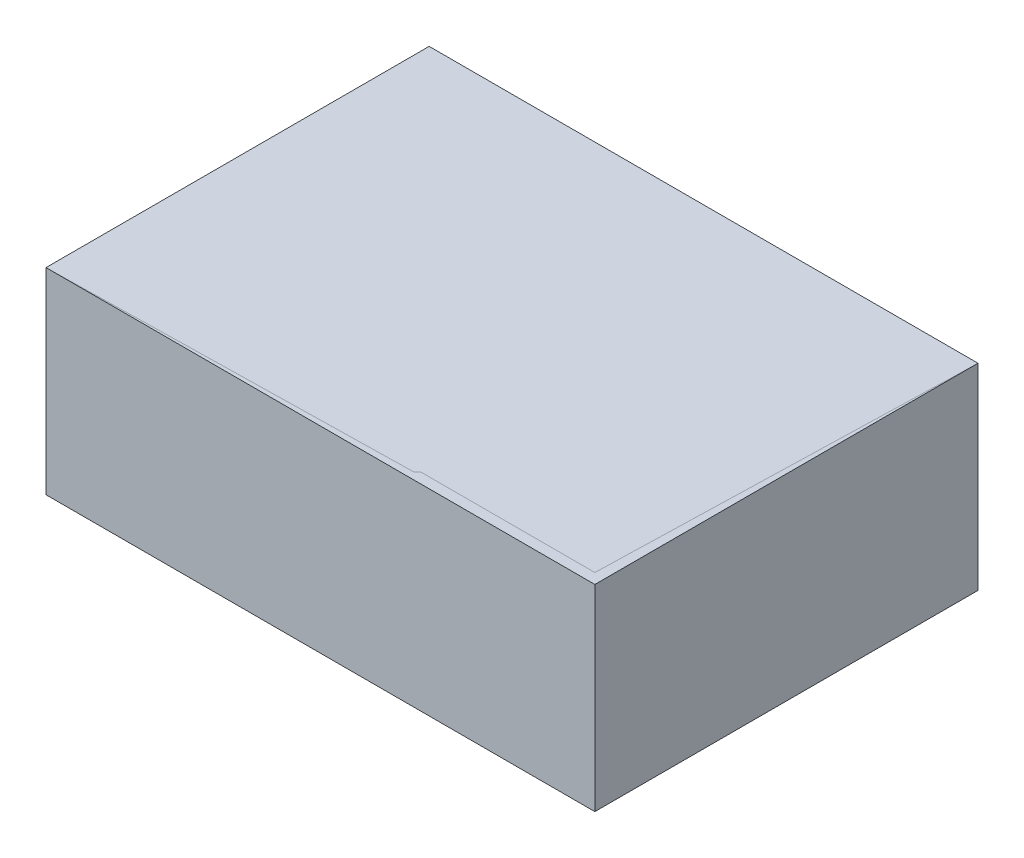
SolidWorks part; units mm, degrees
ref_plane "Front Plane" through (0, 0, 0) normal (0, 0, 1) x (1, 0, 0)
ref_plane "Top Plane" through (0, 0, 0) normal (0, 1, 0) x (1, 0, 0)
ref_plane "Right Plane" through (0, 0, 0) normal (1, 0, 0) x (0, 0, -1)
sketch "Sketch1" plane through (0, 0, 0) normal (0, 1, 0) x (1, 0, 0)
  line L1 (-132.5, -92.5) -> (132.5, -92.5)
  line L2 (-132.5, -92.5) -> (-132.5, 92.5)
  line L3 (-132.5, 92.5) -> (132.5, 92.5)
  line L4 (132.5, -92.5) -> (132.5, 92.5)
  line L5 (-132.5, -92.5) -> (132.5, 92.5) construction
  line L6 (-132.5, 92.5) -> (132.5, -92.5) construction
  point P0 (0, 0)
  dimension "D1" = 265
  dimension "D2" = 185
extrude "Boss-Extrude1" add sketch "Sketch1" along normal blind 95
sketch "Sketch2" plane through (0, 95, 0) normal (0, 1, 0) x (1, 0, 0)
  line L1 (-127.5, -87.5) -> (127.5, -87.5)
  line L2 (-127.5, -87.5) -> (-127.5, 87.5)
  line L3 (-127.5, 87.5) -> (127.5, 87.5)
  line L4 (127.5, -87.5) -> (127.5, 87.5)
  line L5 (-127.5, -87.5) -> (127.5, 87.5) construction
  line L6 (-127.5, 87.5) -> (127.5, -87.5) construction
  point P0 (0, 0)
  dimension "D1" = 255
  dimension "D2" = 175
extrude "Cut-Extrude1" cut sketch "Sketch2" against normal blind 85
sketch "Sketch5" plane through (0, 95, 0) normal (0, 1, 0) x (1, 0, 0)
  line L4 (132.5, -92.5) -> (132.5, 92.5)
  line L5 (132.5, 92.5) -> (-132.5, 92.5)
  line L6 (-132.5, 92.5) -> (-132.5, -92.5)
  line L7 (-132.5, -92.5) -> (132.5, -92.5)
  line L8 (132.5, -92.5) -> (132.5, 92.5)
  line L9 (132.5, 92.5) -> (-132.5, 92.5)
  line L10 (-132.5, 92.5) -> (-132.5, -92.5)
  line L11 (-132.5, -92.5) -> (132.5, -92.5)
  dimension "D1" = 0
surface "Surface-Plane1" sketch "Sketch5"
